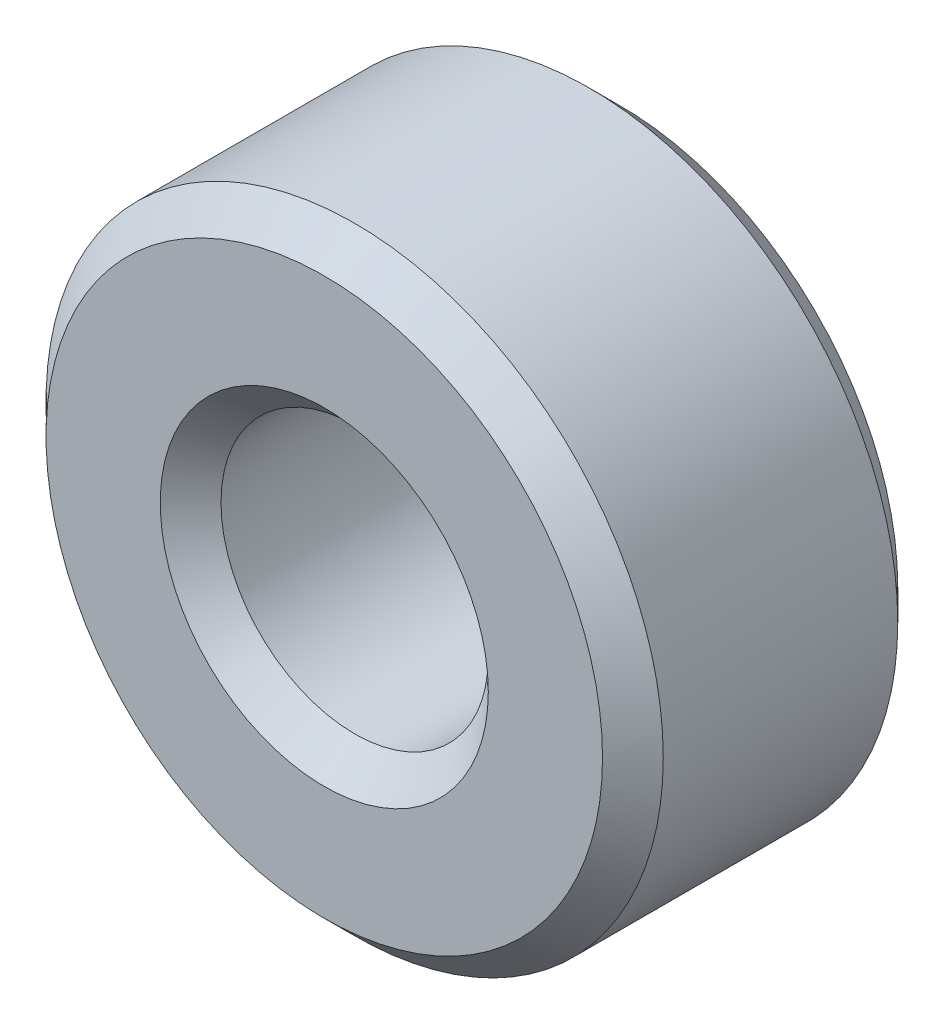
SolidWorks part; units mm, degrees
ref_plane "Plano frontal" through (0, 0, 0) normal (0, 0, 1) x (1, 0, 0)
ref_plane "Plano superior" through (0, 0, 0) normal (0, 1, 0) x (1, 0, 0)
ref_plane "Plano direito" through (0, 0, 0) normal (1, 0, 0) x (0, 0, -1)
sketch "Esboço1" plane through (0, 0, 0) normal (0, 0, 1) x (1, 0, 0)
  circle A0 centre (0, 0) radius 25.4
  circle A1 centre (0, 0) radius 11
  dimension "D1" = 22
  dimension "D2" = 50.8
extrude "Ressalto-extrusão1" add sketch "Esboço1" along normal blind 24.3
chamfer "Chanfro1" distance 2.5 angle 45 4 edges at (11, 0, 0) (11, 0, 24.3) (25.4, 0, 0) (25.4, 0, 24.3)
